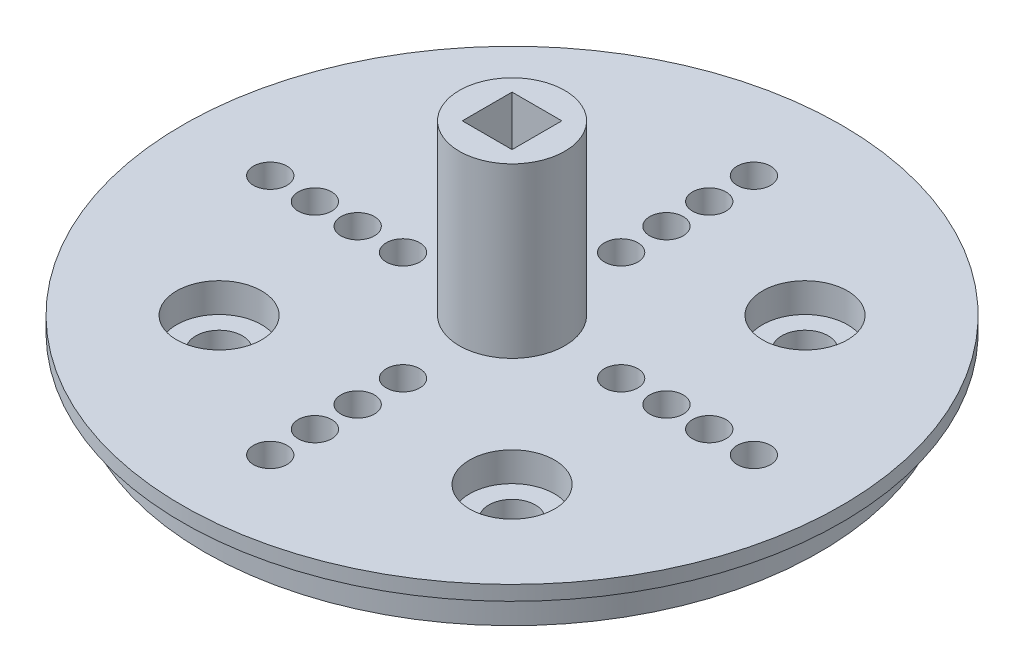
SolidWorks part; units mm, degrees
other "DetailItem1"
ref_plane "Front Plane" through (0, 0, 0) normal (0, 0, 1) x (1, 0, 0)
ref_plane "Top Plane" through (0, 0, 0) normal (0, 1, 0) x (1, 0, 0)
ref_plane "Right Plane" through (0, 0, 0) normal (1, 0, 0) x (0, 0, -1)
sketch "Sketch2" plane through (0, 0, 0) normal (0, 1, 0) x (1, 0, 0)
  circle A0 centre (0, 0) radius 21
extrude "Boss-Extrude1" add sketch "Sketch2" along normal blind 3.5
sketch "Sketch1" plane through (0, 0, 0) normal (0, 1, 0) x (1, 0, 0)
  line L0 (-19.41, 0) -> (20, 0) construction
  line L1 (0, 20) -> (0, -20) construction
  line L2 (-2.3825, -18.9992) -> (-4.4832, -6.5648)
  line L3 (2.3825, -18.9992) -> (4.4832, -6.5648)
  line L4 (-18.9992, 2.3825) -> (-6.5648, 4.4832)
  line L5 (-18.9992, -2.3825) -> (-6.5648, -4.4832)
  line L6 (18.9992, -2.3825) -> (6.5648, -4.4832)
  line L7 (18.9992, 2.3825) -> (6.5648, 4.4832)
  line L8 (2.3825, 18.9992) -> (4.4832, 6.5648)
  line L9 (-2.3825, 18.9992) -> (-4.4832, 6.5648)
  circle A0 centre (0, 0) radius 20 construction
  circle A1 centre (0, 0) radius 3.6 construction
  arc A2 (18.9992, -2.3825) -> (18.9992, 2.3825) centre (16.6638, 0) ccw
  arc A3 (-2.3825, -18.9992) -> (2.3825, -18.9992) centre (0, -16.6638) ccw
  arc A4 (-18.9992, 2.3825) -> (-18.9992, -2.3825) centre (-16.6638, 0) ccw
  arc A5 (2.3825, 18.9992) -> (-2.3825, 18.9992) centre (0, 16.6638) ccw
  arc A6 (4.4832, -6.5648) -> (6.5648, -4.4832) centre (6.988, -6.988) cw
  arc A7 (6.5648, 4.4832) -> (4.4832, 6.5648) centre (6.988, 6.988) cw
  arc A8 (-4.4832, 6.5648) -> (-6.5648, 4.4832) centre (-6.988, 6.988) cw
  arc A9 (-6.5648, -4.4832) -> (-4.4832, -6.5648) centre (-6.988, -6.988) cw
  point P27 (0, 0)
  point P52 (0, 0)
  dimension "D1" = 4
sketch "Sketch4" plane through (0, 3.5, 0) normal (0, 1, 0) x (1, 0, 0)
  line L0 (0, 21) -> (0, -21) construction
  line L1 (-21, 0) -> (21, 0) construction
  circle A0 centre (0, 0) radius 21 construction
  circle A1 centre (0, 0) radius 5.5
  circle A2 centre (7.445, 0) radius 1.143
  circle A3 centre (10.54, 0) radius 1.143
  circle A4 centre (13.46, 0) radius 1.143
  circle A5 centre (16.51, 0) radius 1.143
  circle A6 centre (10, 10) radius 1.5875
  circle A7 centre (0, -7.445) radius 1.143
  circle A8 centre (0, -10.54) radius 1.143
  circle A9 centre (0, -13.46) radius 1.143
  circle A10 centre (0, -16.51) radius 1.143
  circle A11 centre (10, -10) radius 1.5875
  circle A12 centre (-7.445, 0) radius 1.143
  circle A13 centre (-10.54, 0) radius 1.143
  circle A14 centre (-13.46, 0) radius 1.143
  circle A15 centre (-16.51, 0) radius 1.143
  circle A16 centre (-10, -10) radius 1.5875
  circle A17 centre (0, 7.445) radius 1.143
  circle A18 centre (0, 10.54) radius 1.143
  circle A19 centre (0, 13.46) radius 1.143
  circle A20 centre (0, 16.51) radius 1.143
  circle A21 centre (-10, 10) radius 1.5875
  point P52 (0, 0)
  dimension "D1" = 4
extrude "Cut-Extrude2" cut sketch "Sketch4" against normal through all
sketch "Sketch5" plane through (0, 3.5, 0) normal (0, 1, 0) x (1, 0, 0)
  circle A0 centre (-10, 10) radius 2.9
  circle A1 centre (-10, -10) radius 2.9
  circle A2 centre (10, 10) radius 2.9
  circle A3 centre (10, -10) radius 2.9
extrude "Cut-Extrude4" cut sketch "Sketch5" against normal blind 2
sketch "Sketch6" plane through (0, 0, 0) normal (0, 0, 1) x (1, 0, 0)
  line L0 (21, 3.5) -> (-21, 3.5) construction
  line L1 (-20.3515, 3.5) -> (-22.5, 3.5)
  line L2 (-20.3515, 3.5) -> (-20.3515, 2.5)
  line L3 (-20.3515, 2.5) -> (-22.5, 2.5)
  line L4 (-22.5, 3.5) -> (-22.5, 2.5)
  line L5 (-21, 3.5) -> (-21, 0) construction
  line L6 (0, 0) -> (0, 5.1601) construction
  dimension "D1" = 1
  dimension "D2" = 1.5
revolve "Revolve1" add sketch "Sketch6" angle 360 about L6
sketch "Sketch7" plane through (0, 3.5, 0) normal (0, 1, 0) x (1, 0, 0)
  circle A0 centre (0, 0) radius 6.25
sketch "Sketch8" plane through (0, 0, 0) normal (0, 1, 0) x (1, 0, 0)
  line L1 (1.7, -1.7) -> (1.7, 1.7)
  line L2 (1.7, 1.7) -> (-1.7, 1.7)
  line L3 (-1.7, 1.7) -> (-1.7, -1.7)
  line L4 (-1.7, -1.7) -> (1.7, -1.7)
  circle A0 centre (0, 0) radius 1.7 construction
  circle A1 centre (0, 0) radius 3.6
extrude "Boss-Extrude3" add sketch "Sketch8" along normal blind 15
extrude "Boss-Extrude4" add sketch "Sketch7" against normal blind 2.5 contours A0
